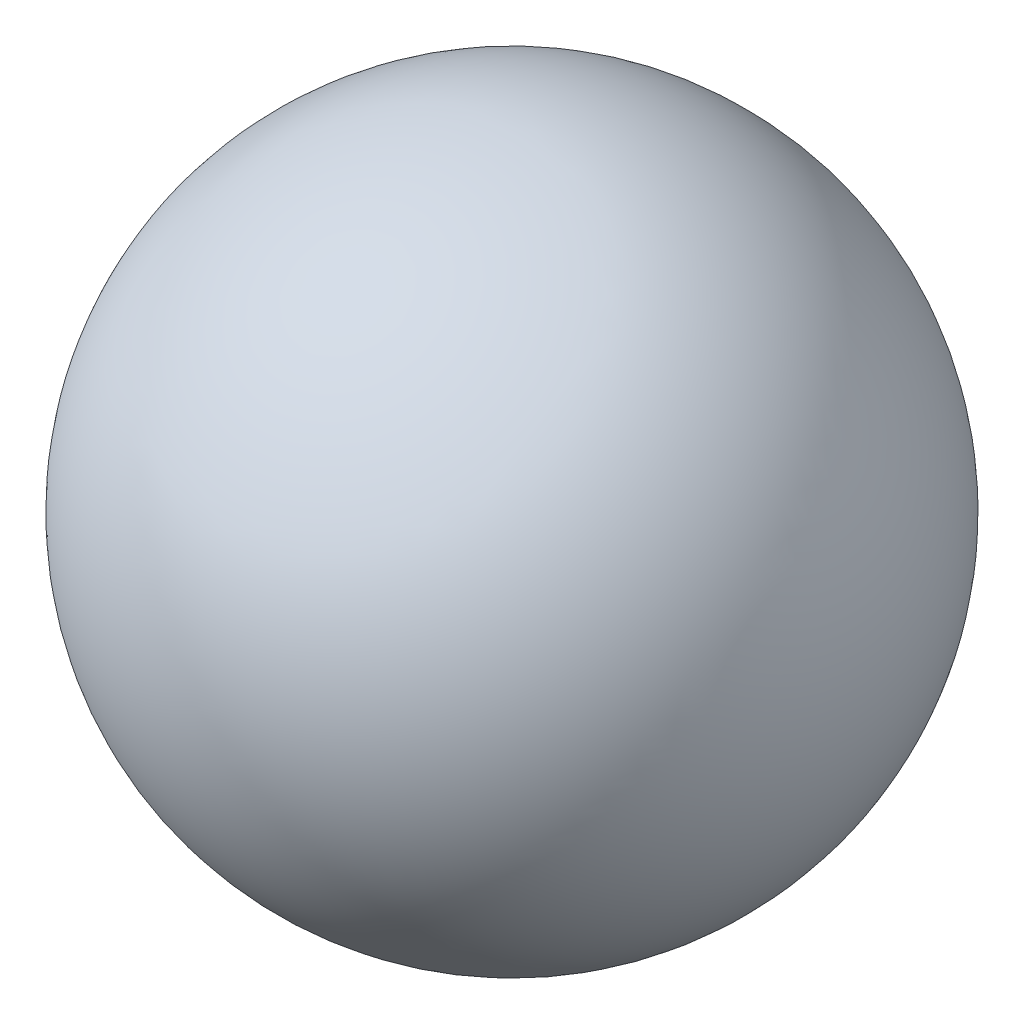
SolidWorks part; units mm, degrees
ref_plane "Plane1" through (0, 0, 0) normal (0, 0, 1) x (1, 0, 0)
ref_plane "Plane2" through (0, 0, 0) normal (0, 1, 0) x (1, 0, 0)
ref_plane "Plane3" through (0, 0, 0) normal (1, 0, 0) x (0, 0, -1)
sketch "Эскиз3" plane through (0, 0, 0) normal (0, 0, 1) x (1, 0, 0)
  line L0 (-2000, 0) -> (2000, 0) construction
  line L1 (-1000, 0) -> (1000, 0)
  arc A0 (-1000, 0) -> (1000, 0) centre (0, 0) cw
revolve "Основание-Повернуть" add sketch "Эскиз3" angle 360 about L0
